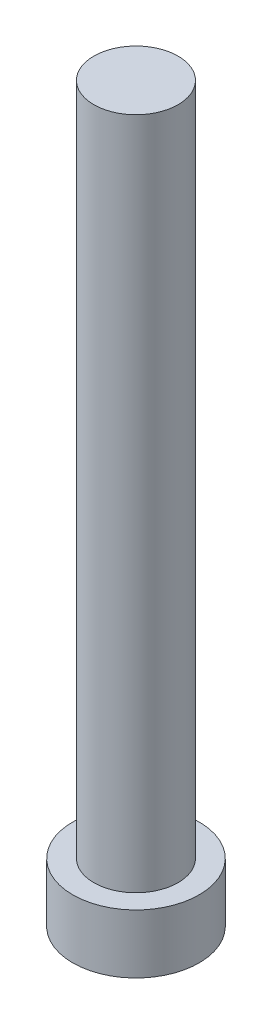
SolidWorks part; units mm, degrees
ref_plane "Front Plane" through (0, 0, 0) normal (0, 0, 1) x (1, 0, 0)
ref_plane "Top Plane" through (0, 0, 0) normal (0, 1, 0) x (1, 0, 0)
ref_plane "Right Plane" through (0, 0, 0) normal (1, 0, 0) x (0, 0, -1)
sketch "Sketch1" plane through (0, 0, 0) normal (0, 1, 0) x (1, 0, 0)
  circle A0 centre (0, 0) radius 3.75
  dimension "D1" = 7.5
extrude "Boss-Extrude1" add sketch "Sketch1" along normal blind 3.5
sketch "Sketch2" plane through (0, 3.5, 0) normal (0, 1, 0) x (1, 0, 0)
  circle A0 centre (0, 0) radius 2.5
  dimension "D1" = 5
extrude "Boss-Extrude2" add sketch "Sketch2" along normal blind 40
